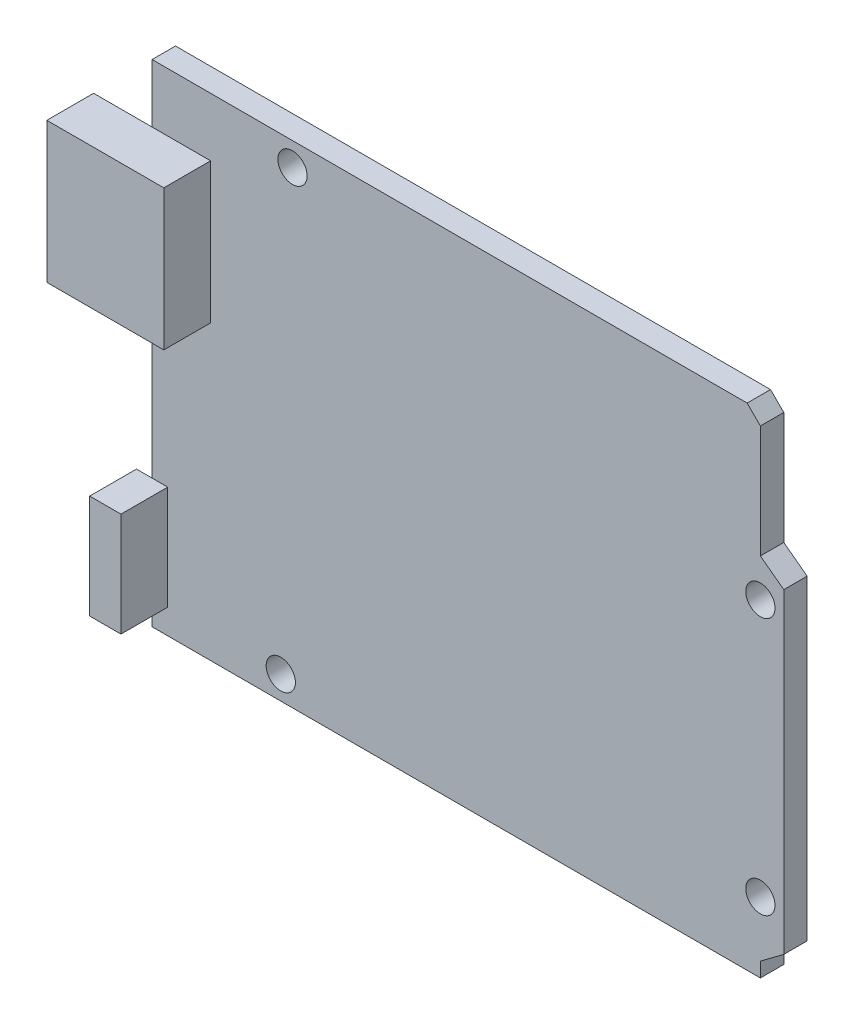
SolidWorks part; units mm, degrees
ref_plane "Front Plane" through (0, 0, 0) normal (0, 0, 1) x (1, 0, 0)
ref_plane "Top Plane" through (0, 0, 0) normal (0, 1, 0) x (1, 0, 0)
ref_plane "Right Plane" through (0, 0, 0) normal (1, 0, 0) x (0, 0, -1)
sketch "Sketch1" plane through (0, 0, 0) normal (0, 0, 1) x (1, 0, 0)
  line L1 (-34.29, -26.67) -> (34.29, -26.67)
  line L2 (-34.29, -26.67) -> (-34.29, 26.67)
  line L3 (-34.29, 26.67) -> (34.29, 26.67)
  line L4 (34.29, -26.67) -> (34.29, 26.67)
  line L5 (-34.29, -26.67) -> (34.29, 26.67) construction
  line L6 (-34.29, 26.67) -> (34.29, -26.67) construction
  point P0 (0, 0)
  dimension "D1" = 68.58
  dimension "D2" = 53.34
extrude "Boss-Extrude1" add sketch "Sketch1" along normal blind 2.54
sketch "Sketch2" plane through (0, 0, 2.54) normal (0, 0, 1) x (1, 0, 0)
  line L0 (-34.29, 26.67) -> (-34.29, -26.67) construction
  line L1 (-40.64, 5.08) -> (-27.94, 5.08)
  line L2 (-40.64, 5.08) -> (-40.64, 20.32)
  line L3 (-40.64, 20.32) -> (-27.94, 20.32)
  line L4 (-27.94, 5.08) -> (-27.94, 20.32)
  line L5 (-40.64, 5.08) -> (-27.94, 20.32) construction
  line L6 (-40.64, 20.32) -> (-27.94, 5.08) construction
  line L7 (34.29, 26.67) -> (-34.29, 26.67) construction
  line L9 (-35.9875, -23.9716) -> (-32.5925, -23.9716)
  line L10 (-35.9875, -23.9716) -> (-35.9875, -12.686)
  line L11 (-35.9875, -12.686) -> (-32.5925, -12.686)
  line L12 (-32.5925, -23.9716) -> (-32.5925, -12.686)
  line L13 (-35.9875, -23.9716) -> (-32.5925, -12.686) construction
  line L14 (-35.9875, -12.686) -> (-32.5925, -23.9716) construction
  point P0 (-34.29, 12.7)
  point P9 (-34.29, -18.3288)
  dimension "D1" = 12.7
  dimension "D2" = 15.24
  dimension "D3" = 6.35
extrude "Boss-Extrude2" add sketch "Sketch2" along normal blind 5.08
sketch "Sketch3" plane through (0, 0, 2.54) normal (0, 0, 1) x (1, 0, 0)
  line L0 (-34.29, -26.67) -> (34.29, -26.67) construction
  line L1 (-34.29, 5.08) -> (-34.29, -12.686) construction
  circle A0 centre (-19.05, 24.13) radius 1.5875
  circle A1 centre (-20.32, -24.13) radius 1.5875
  circle A2 centre (31.75, 8.89) radius 1.5875
  circle A3 centre (31.75, -19.05) radius 1.5875
  point P8 (0, 0)
  point P11 (0, 0)
  dimension "D1" = 3.175
  dimension "D2" = 1.27
  dimension "D3" = 50.8
  dimension "D4" = 5.08
  dimension "D5" = 2.54
  dimension "D6" = 27.94
  dimension "D7" = 15.24
  dimension "D8" = 13.97
extrude "Cut-Extrude1" cut sketch "Sketch3" against normal blind 10.16
sketch "Sketch4" plane through (0, 0, 2.54) normal (0, 0, 1) x (1, 0, 0)
  line L0 (30.3132, 26.67) -> (31.75, 25.2332)
  line L1 (34.29, 26.67) -> (-34.29, 26.67) construction
  line L3 (31.75, 13.0127) -> (34.29, 11.1158)
  line L4 (34.29, -26.67) -> (34.29, 26.67) construction
  line L5 (34.29, 11.1158) -> (34.29, 26.67)
  line L6 (34.29, 26.67) -> (30.3132, 26.67)
  line L7 (34.29, -23.1815) -> (31.75, -25.0785)
  line L8 (31.75, 13.0127) -> (31.75, 25.2332)
  line L9 (31.75, -25.0785) -> (31.75, -26.67)
  line L10 (-34.29, -26.67) -> (34.29, -26.67) construction
  line L11 (31.75, -26.67) -> (34.29, -26.67)
  line L12 (34.29, -26.67) -> (34.29, -23.1815)
  point P4 (0, 0)
  point P12 (0, 0)
  point P18 (33.02, -24.13)
  dimension "D1" = 45
  dimension "D2" = 2.032
  dimension "D3" = 2.54
extrude "Cut-Extrude2" cut sketch "Sketch4" against normal through all
